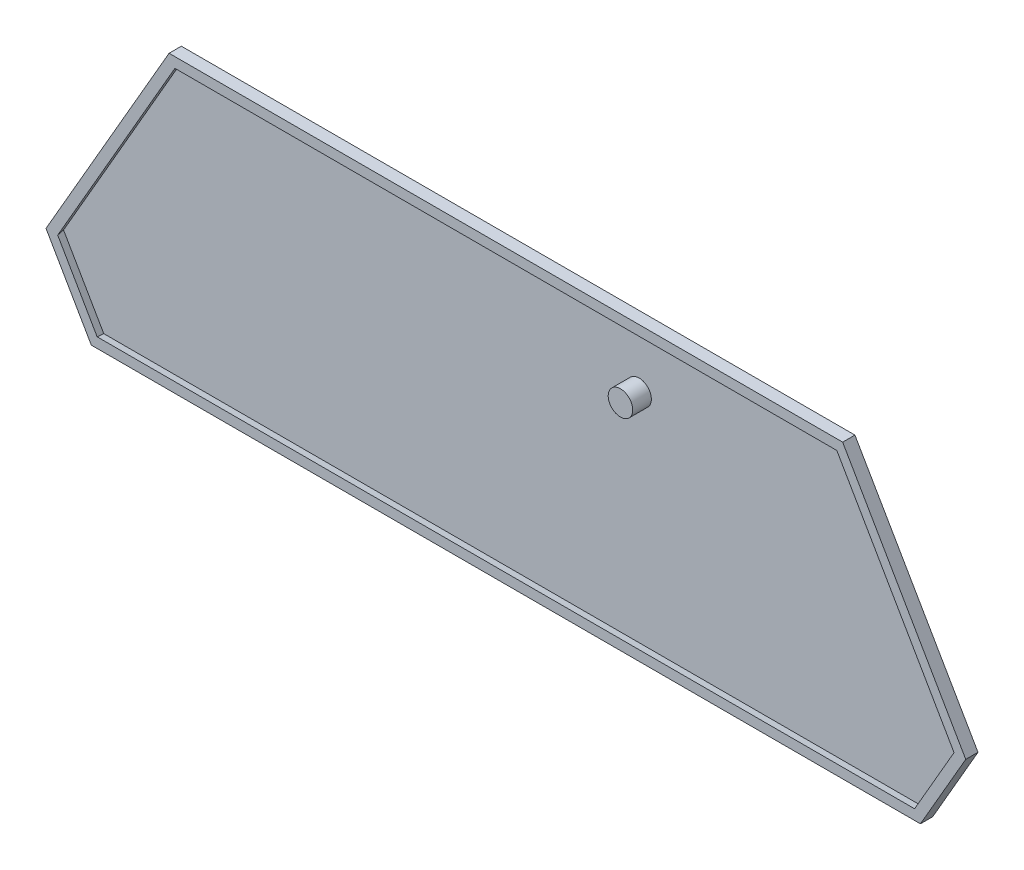
SolidWorks part; units mm, degrees
ref_plane "Plan de face" through (0, 0, 0) normal (0, 0, 1) x (1, 0, 0)
ref_plane "Plan de dessus" through (0, 0, 0) normal (0, 1, 0) x (1, 0, 0)
ref_plane "Plan de droite" through (0, 0, 0) normal (1, 0, 0) x (0, 0, -1)
sketch "Esquisse1" plane through (0, 0, 0) normal (0, 0, 1) x (1, 0, 0)
  line L6 (-84.5248, -59.4671) -> (-2.7, -59.4671) construction
  line L7 (68.6667, 0) -> (-68.6667, 0) construction
  line L8 (-68.6667, 0) -> (-93.7624, -43.4671) construction
  line L9 (-93.7624, -43.4671) -> (-84.5248, -59.4671) construction
  line L10 (84.5248, -59.4671) -> (93.7624, -43.4671) construction
  line L11 (93.7624, -43.4671) -> (68.6667, 0) construction
  line L12 (2.7, -59.4671) -> (84.5248, -59.4671) construction
  line L70 (-84.5248, -59.4671) -> (2.7, -59.4671)
  line L71 (-93.7624, -43.4671) -> (-84.5248, -59.4671)
  line L72 (-68.6667, 0) -> (-93.7624, -43.4671)
  line L73 (68.6667, 0) -> (-68.6667, 0)
  line L74 (93.7624, -43.4671) -> (68.6667, 0)
  line L75 (84.5248, -59.4671) -> (93.7624, -43.4671)
  line L76 (2.7, -59.4671) -> (84.5248, -59.4671)
extrude "Boss.-Extru.1" add sketch "Esquisse1" along normal blind 1
sketch "Esquisse2" plane through (0, 0, 1) normal (0, 0, 1) x (1, 0, 0)
  line L6 (-93.7624, -43.4671) -> (-84.5248, -59.4671)
  line L7 (-84.5248, -59.4671) -> (84.5248, -59.4671)
  line L8 (84.5248, -59.4671) -> (93.7624, -43.4671)
  line L9 (93.7624, -43.4671) -> (68.6667, 0)
  line L10 (68.6667, 0) -> (-68.6667, 0)
  line L11 (-68.6667, 0) -> (-93.7624, -43.4671)
  line L12 (-93.7624, -43.4671) -> (-84.5248, -59.4671)
  line L13 (-84.5248, -59.4671) -> (84.5248, -59.4671)
  line L14 (84.5248, -59.4671) -> (93.7624, -43.4671)
  line L15 (93.7624, -43.4671) -> (68.6667, 0)
  line L16 (68.6667, 0) -> (-68.6667, 0)
  line L17 (-68.6667, 0) -> (-93.7624, -43.4671)
  dimension "D1" = 0
extrude "Extru.-Mince1" add sketch "Esquisse2" along normal blind 1.5 draft 10 thin thin type one direction reverse wall 1.8 draft outward yes
sketch "Esquisse3" plane through (0, 0, 0) normal (0, 0, -1) x (-1, 0, 0)
  line L6 (84.5248, -59.4671) -> (93.7624, -43.4671)
  line L7 (93.7624, -43.4671) -> (68.6667, 0)
  line L8 (68.6667, 0) -> (-68.6667, 0)
  line L9 (-68.6667, 0) -> (-93.7624, -43.4671)
  line L10 (-93.7624, -43.4671) -> (-84.5248, -59.4671)
  line L11 (-84.5248, -59.4671) -> (84.5248, -59.4671)
  line L12 (84.5248, -59.4671) -> (93.7624, -43.4671)
  line L13 (93.7624, -43.4671) -> (68.6667, 0)
  line L14 (68.6667, 0) -> (-68.6667, 0)
  line L15 (-68.6667, 0) -> (-93.7624, -43.4671)
  line L16 (-93.7624, -43.4671) -> (-84.5248, -59.4671)
  line L17 (-84.5248, -59.4671) -> (84.5248, -59.4671)
  dimension "D1" = 0
extrude "Enlèv. de mat.-Extru.-Mince1" cut sketch "Esquisse3" against normal through all thin
sketch "Esquisse4" plane through (0, 0, 1) normal (0, 0, 1) x (1, 0, 0)
  circle A0 centre (25.6655, -13.4245) radius 2.5
  dimension "D1" = 5
extrude "Boss.-Extru.2" add sketch "Esquisse4" along normal blind 3.8
sketch "Esquisse5" plane through (0, 0, 1) normal (0, 0, 1) x (1, 0, 0)
  line L0 (-18.3, -12.3) -> (-18.3, -16.3)
  line L1 (-18.3, -16.3) -> (-28.5, -16.3)
  line L2 (-28.5, -16.3) -> (-28.5, -12.3)
extrude "Extru.-Mince2" [suppressed] add sketch "Esquisse5" along normal blind 4.5 thin
fillet "Congé1" [suppressed] radius 1
